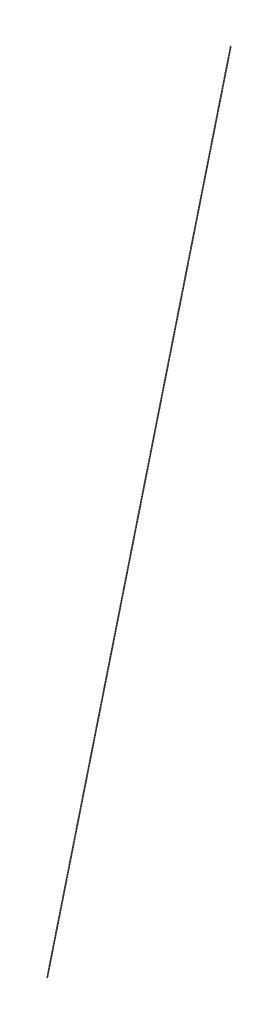
SolidWorks part; units mm, degrees
ref_plane "前视基准面" through (0, 0, 0) normal (0, 0, 1) x (1, 0, 0)
ref_plane "上视基准面" through (0, 0, 0) normal (0, 1, 0) x (1, 0, 0)
ref_plane "右视基准面" through (0, 0, 0) normal (1, 0, 0) x (0, 0, -1)
sketch "草图2" plane through (0, 0, 0) normal (0, 0, 1) x (1, 0, 0)
  line L9 (0, 0) -> (307.5, 1505)
sweep "扫描1" add path "草图2" circular profile diameter 1 parameters "D3"=1
